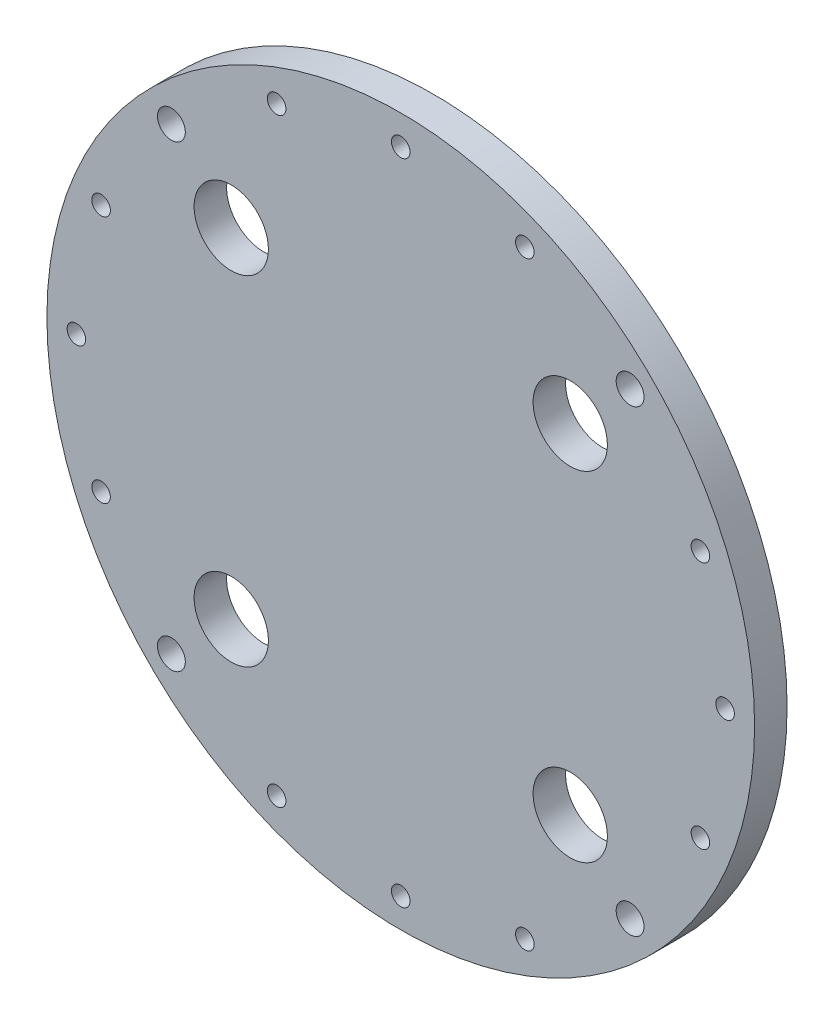
SolidWorks part; units mm, degrees
ref_plane "Front Plane" through (0, 0, 0) normal (0, 0, 1) x (1, 0, 0)
ref_plane "Top Plane" through (0, 0, 0) normal (0, 1, 0) x (1, 0, 0)
ref_plane "Right Plane" through (0, 0, 0) normal (1, 0, 0) x (0, 0, -1)
sketch "Sketch1" plane through (0, 0, 0) normal (0, 0, 1) x (1, 0, 0)
  line L0 (0, 70.5725) -> (0, 76.2) construction
  line L3 (-1.25, 69.3225) -> (12.2983, 69.3225) construction
  circle A0 centre (0, 0) radius 63.5
  circle A1 centre (0, 0) radius 76.2
  circle A2 centre (0, 69.3225) radius 1.25 construction
  circle A3 centre (69.3225, 0) radius 1.25 construction
  circle A4 centre (0, -69.3225) radius 1.25 construction
  circle A5 centre (-69.3225, 0) radius 1.25 construction
  point P19 (0, 0)
  dimension "D1" = 127
  dimension "D2" = 152.4
  dimension "D3" = 2.5
  dimension "D5" = 5.6275
  dimension "D4" = 4
extrude "Boss-Extrude1" add sketch "Sketch1" along normal blind 28.225
sketch "Sketch2" plane through (0, 0, 0) normal (0, 0, -1) x (-1, 0, 0)
  circle A0 centre (0, 69.3225) radius 2.5
  circle A1 centre (69.3225, 0) radius 2.5
  circle A2 centre (0, -69.3225) radius 2.5
  circle A3 centre (-69.3225, 0) radius 2.5
  point P3 (0, 0)
  point P12 (0, 0)
  dimension "D1" = 5
  dimension "D2" = 4
extrude "Cut-Extrude1" [suppressed] cut sketch "Sketch2" against normal blind 6.725
sketch "Sketch3" plane through (0, 0, 28.225) normal (0, 0, 1) x (1, 0, 0)
  line L0 (0, 69.3225) -> (0, 0) construction
  line L1 (0, 0) -> (-79.0122, 79.0122) construction
  line L2 (-53.8815, 53.8815) -> (-53.8815, 44.9013) construction
  line L3 (-53.8815, 44.9013) -> (-44.9013, 44.9013) construction
  line L4 (-53.8815, 44.9013) -> (-46.9345, 51.8484) construction
  circle A0 centre (0, 0) radius 76.2 construction
  circle A1 centre (0, 0) radius 63.5 construction
  circle A2 centre (-49.3914, 49.3914) radius 3
  circle A3 centre (49.3914, 49.3914) radius 3
  circle A4 centre (49.3914, -49.3914) radius 3
  circle A5 centre (-49.3914, -49.3914) radius 3
  point P16 (0, 0)
  point P17 (0, 0)
  point P18 (0, 0)
  point P25 (0, 0)
  dimension "D2" = 6
  dimension "D1" = 45
  dimension "D3" = 4
extrude "Cut-Extrude2" cut sketch "Sketch3" against normal through all
sketch "Sketch4" plane through (0, 0, 28.225) normal (0, 0, 1) x (1, 0, 0)
  circle A0 centre (0, 0) radius 107.9579
extrude "Cut-Extrude3" cut sketch "Sketch4" against normal blind 10.225
sketch "Sketch5" plane through (0, 0, 0) normal (0, 0, -1) x (-1, 0, 0)
  circle A0 centre (0, 0) radius 63.5
  circle A1 centre (0, 0) radius 56.5
  circle A2 centre (0, 0) radius 63.5 construction
  dimension "D1" = 7
extrude "Boss-Extrude2" [suppressed] add sketch "Sketch5" along normal blind 55.225 separate body
sketch "Sketch6" [suppressed] plane through (0, 0, -55.225) normal (0, 0, -1) x (-1, 0, 0)
  circle A0 centre (0, 0) radius 56.5
extrude "Boss-Extrude3" [suppressed] add sketch "Sketch6" against normal blind 7
sketch "Sketch7" plane through (0, 0, 0) normal (0, 0, -1) x (-1, 0, 0)
  line L0 (0, 76.2) -> (0, 63.5) construction
  line L1 (0, 63.5) -> (-8.1249, 69.85) construction
  line L2 (-8.1249, 69.85) -> (0, 76.2) construction
  line L3 (-8.1249, 69.85) -> (0, 69.85) construction
  circle A0 centre (0, 69.85) radius 2
  circle A1 centre (0, 0) radius 76.2 construction
  circle A2 centre (0, 0) radius 63.5 construction
  circle A3 centre (69.85, 0) radius 2
  circle A4 centre (0, -69.85) radius 2
  circle A5 centre (-69.85, 0) radius 2
  point P20 (0, 0)
  dimension "D1" = 4
  dimension "D2" = 4
extrude "Cut-Extrude4" cut sketch "Sketch7" against normal blind 11
sketch "Sketch8" plane through (0, 0, 0) normal (0, 0, -1) x (-1, 0, 0)
  circle A0 centre (0, 69.85) radius 1
  circle A1 centre (69.85, 0) radius 1
  circle A2 centre (0, -69.85) radius 1
  circle A3 centre (-69.85, 0) radius 1
  point P12 (0, 0)
  dimension "D1" = 2
  dimension "D2" = 4
extrude "Cut-Extrude5" cut sketch "Sketch8" against normal through all
sketch "Sketch9" plane through (0, 0, 18) normal (0, 0, 1) x (1, 0, 0)
  circle A0 centre (0, 0) radius 92.0633
extrude "Cut-Extrude6" cut sketch "Sketch9" against normal blind 11
sketch "Sketch10" plane through (0, 0, 7) normal (0, 0, 1) x (1, 0, 0)
  line L0 (0, 0) -> (-69.85, 0) construction
  line L1 (0, 0) -> (-64.533, 26.7304) construction
  line L2 (0, 0) -> (-64.533, -26.7304) construction
  circle A0 centre (-64.533, 26.7304) radius 2
  circle A1 centre (-64.533, -26.7304) radius 2
  circle A2 centre (-69.85, 0) radius 2 construction
  circle A3 centre (26.7304, 64.533) radius 2
  circle A4 centre (-26.7304, 64.533) radius 2
  circle A5 centre (64.533, -26.7304) radius 2
  circle A6 centre (64.533, 26.7304) radius 2
  circle A7 centre (-26.7304, -64.533) radius 2
  circle A8 centre (26.7304, -64.533) radius 2
  point P25 (0, 0)
  dimension "D1" = 22.5
  dimension "D2" = 22.5
  dimension "D3" = 4
extrude "Cut-Extrude7" cut sketch "Sketch10" against normal through all
sketch "Sketch11" plane through (0, 0, 7) normal (0, 0, 1) x (1, 0, 0)
  circle A0 centre (0, 0) radius 63.5 construction
  circle A1 centre (0, 0) radius 63.5
extrude "Boss-Extrude5" add sketch "Sketch11" against normal up to surface (7 mm away) up to face at (66.533, -26.7304, 0)
sketch "Sketch12" plane through (0, 0, 7) normal (0, 0, 1) x (1, 0, 0)
  line L1 (36.5, -36.5) -> (-36.5, -36.5) construction
  line L2 (36.5, -36.5) -> (36.5, 36.5) construction
  line L3 (36.5, 36.5) -> (-36.5, 36.5) construction
  line L4 (-36.5, -36.5) -> (-36.5, 36.5) construction
  line L5 (36.5, -36.5) -> (-36.5, 36.5) construction
  line L6 (36.5, 36.5) -> (-36.5, -36.5) construction
  circle A0 centre (-36.5, 36.5) radius 8
  circle A1 centre (36.5, 36.5) radius 8
  circle A2 centre (-36.5, -36.5) radius 8
  circle A3 centre (36.5, -36.5) radius 8
  point P0 (0, 0)
  dimension "D2" = 16
  dimension "D1" = 73
extrude "Cut-Extrude8" cut sketch "Sketch12" against normal up to surface (7 mm away) up to face at (66.533, -26.7304, 0)
